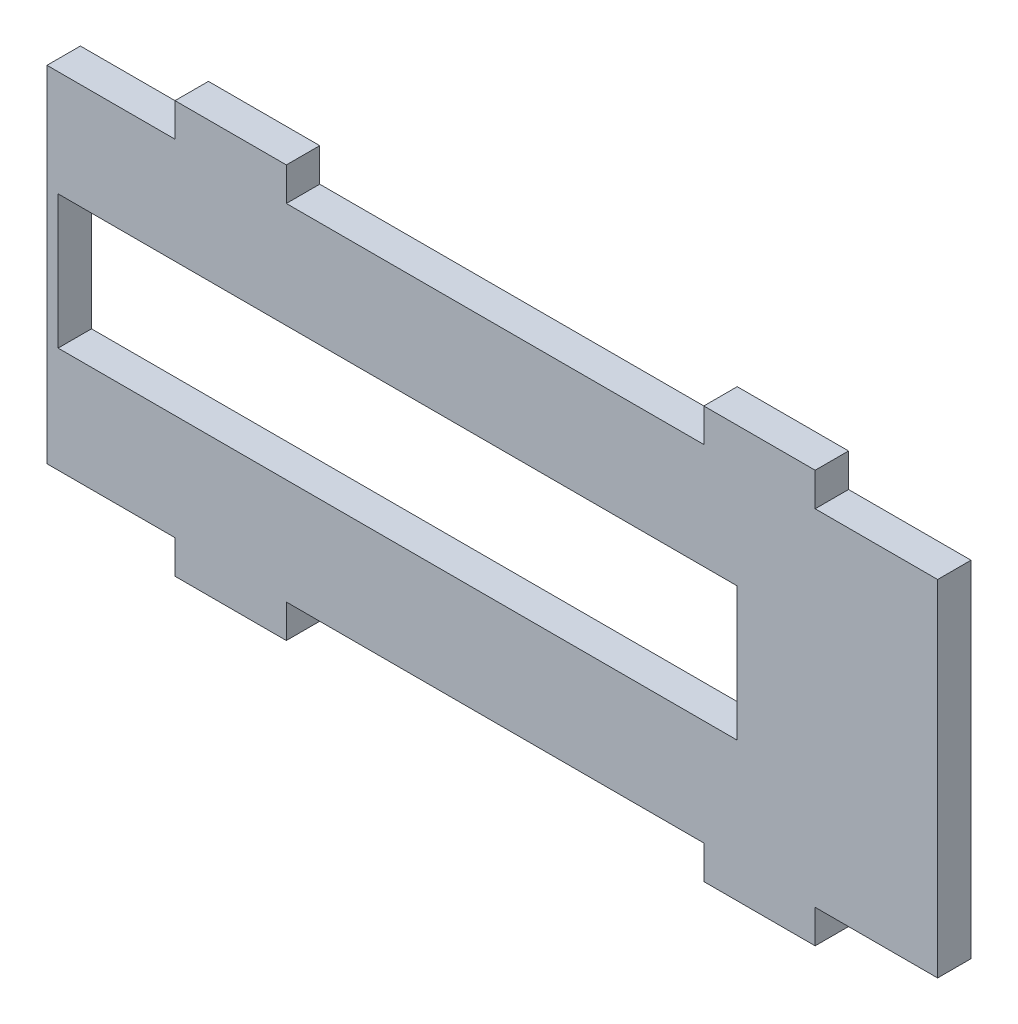
SolidWorks part; units mm, degrees
ref_plane "前视基准面" through (0, 0, 0) normal (0, 0, 1) x (1, 0, 0)
ref_plane "上视基准面" through (0, 0, 0) normal (0, 1, 0) x (1, 0, 0)
ref_plane "右视基准面" through (0, 0, 0) normal (1, 0, 0) x (0, 0, -1)
sketch "草图1" plane through (0, 0, 0) normal (0, 0, 1) x (1, 0, 0)
  line L0 (0, 15.5) -> (80, 15.5) construction
  line L1 (0, 0) -> (80, 0)
  line L2 (0, 0) -> (0, 31)
  line L3 (0, 31) -> (80, 31)
  line L4 (80, 0) -> (80, 31)
  line L5 (1, 21.5) -> (62, 21.5)
  line L6 (1, 21.5) -> (1, 9.5)
  line L7 (1, 9.5) -> (62, 9.5)
  line L8 (62, 21.5) -> (62, 9.5)
  point P11 (1, 15.5)
  point P12 (0, 0)
  dimension "D1" = 31
  dimension "D2" = 80
  dimension "D3" = 12
  dimension "D4" = 61
  dimension "D5" = 1
extrude "凸台-拉伸1" add sketch "草图1" along normal blind 3
sketch "草图2" plane through (0, 0, 3) normal (0, 0, 1) x (1, 0, 0)
  line L0 (80, 31) -> (0, 31) construction
  line L1 (11.5, 31) -> (21.5, 31)
  line L2 (11.5, 31) -> (11.5, 34)
  line L3 (11.5, 34) -> (21.5, 34)
  line L4 (21.5, 31) -> (21.5, 34)
  line L5 (40.25, 39.1552) -> (40.25, -12.2923) construction
  line L6 (0, 15.5) -> (80, 15.5) construction
  line L7 (0, 31) -> (0, 0) construction
  line L8 (80, 0) -> (80, 31) construction
  line L9 (59, 31) -> (59, 34)
  line L10 (69, 34) -> (59, 34)
  line L11 (69, 31) -> (69, 34)
  line L12 (69, 31) -> (59, 31)
  line L13 (69, 0) -> (59, 0)
  line L14 (69, 0) -> (69, -3)
  line L15 (69, -3) -> (59, -3)
  line L16 (59, 0) -> (59, -3)
  line L17 (21.5, 0) -> (21.5, -3)
  line L18 (11.5, -3) -> (21.5, -3)
  line L19 (11.5, 0) -> (11.5, -3)
  line L20 (11.5, 0) -> (21.5, 0)
  dimension "D1" = 10
  dimension "D2" = 3
  dimension "D3" = 47.5
  dimension "D4" = 11
extrude "凸台-拉伸2" add sketch "草图2" against normal blind 3
